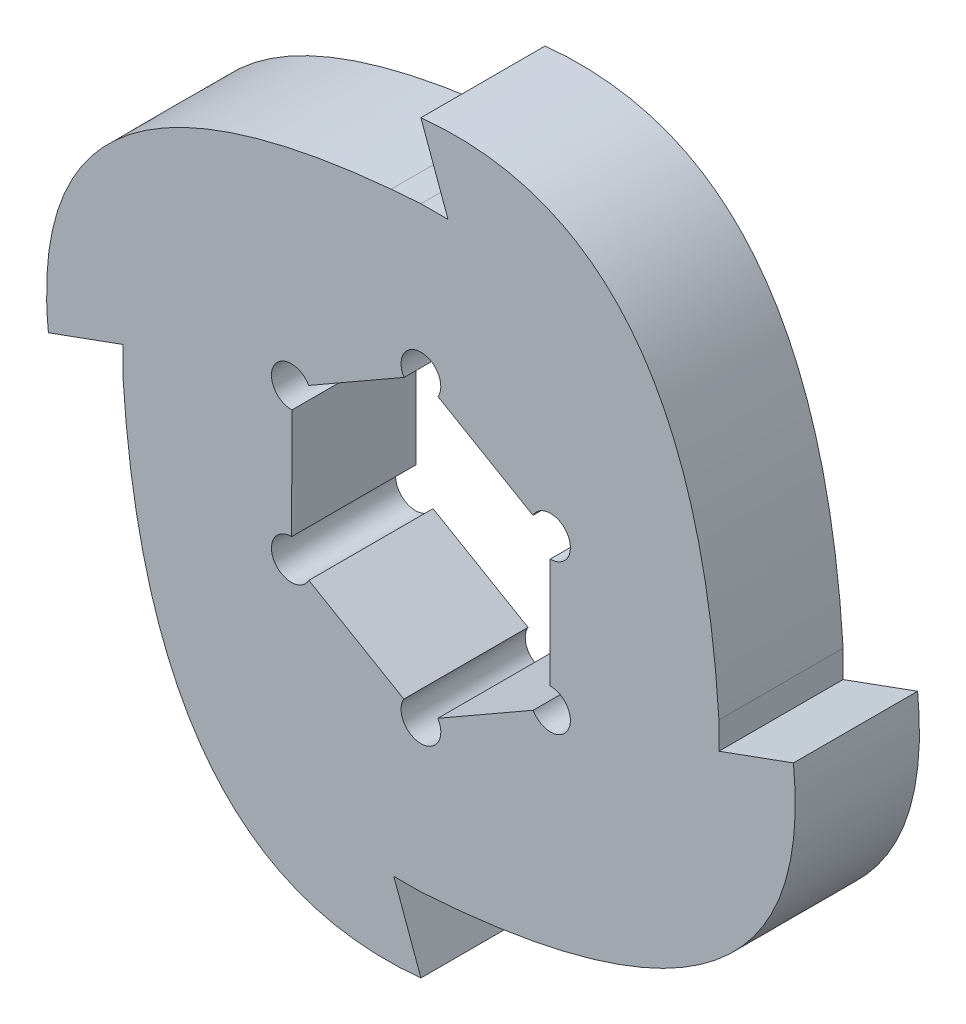
SolidWorks part; units mm, degrees
material "ASTM A36 Steel"
ref_plane "Front Plane" through (0, 0, 0) normal (0, 0, 1) x (1, 0, 0)
ref_plane "Top Plane" through (0, 0, 0) normal (0, 1, 0) x (1, 0, 0)
ref_plane "Right Plane" through (0, 0, 0) normal (1, 0, 0) x (0, 0, -1)
sketch "Sketch1" plane through (0, 0, 0) normal (0, 0, 1) x (1, 0, 0)
  line L0 (0, -1038.1) -> (0, -19.05) construction
  line L1 (6.595, -2.811) -> (6.6131, 2.8106)
  line L2 (5.7319, 4.3059) -> (0.8725, 7.1324)
  line L3 (-0.8631, 7.1169) -> (-5.7406, 4.3218)
  line L4 (-6.595, 2.811) -> (-6.6131, -2.8106)
  line L5 (-5.7319, -4.3059) -> (-0.8725, -7.1324)
  line L6 (0.8631, -7.1169) -> (5.7406, -4.3218)
  line L11 (0, 8.669) -> (0, 15.24) construction
  line L12 (0, 19.05) -> (0, 29.6546) construction
  line L13 (0, -7.653) -> (0, 7.653) construction
  line L14 (-19.05, 0) -> (-15.24, 1.3867)
  line L15 (-15.24, 1.3867) -> (-15.24, 0)
  line L16 (1.3867, 15.24) -> (0, 15.24)
  line L17 (0, 19.05) -> (1.3867, 15.24)
  line L18 (15.24, -1.3867) -> (15.24, 0)
  line L19 (19.05, 0) -> (15.24, -1.3867)
  line L20 (-1.3867, -15.24) -> (0, -15.24)
  line L21 (0, -19.05) -> (-1.3867, -15.24)
  line L22 (0, -15.24) -> (0, -8.669) construction
  circle A0 centre (0, 0) radius 19.05 construction
  circle A1 centre (0, 0) radius 6.604 construction
  arc A2 (-5.7406, 4.3218) -> (-6.595, 2.811) centre (-6.6277, 3.8265) ccw
  arc A3 (0.8725, 7.1324) -> (-0.8631, 7.1169) centre (0, 7.653) ccw
  arc A4 (6.6131, 2.8106) -> (5.7319, 4.3059) centre (6.6277, 3.8265) ccw
  arc A5 (5.7406, -4.3218) -> (6.595, -2.811) centre (6.6277, -3.8265) ccw
  arc A6 (-0.8725, -7.1324) -> (0.8631, -7.1169) centre (0, -7.653) ccw
  arc A7 (-6.6131, -2.8106) -> (-5.7319, -4.3059) centre (-6.6277, -3.8265) ccw
  spline S0 degree 2 poles (-15.24, 0) (-13.9321, -20.4786) (0, -19.05) knots 0 0 0 0.635746 0.635746 0.635746
  spline S1 degree 3 poles (-1.5242, 15.1224) (-14.1243, 13.9761) (-19.9662, 8.9353) (-19.05, 0) knots 0.024149 0.024149 0.024149 0.024149 0.635746 0.635746 0.635746 0.635746
  spline S2 degree 2 poles (15.24, 0) (13.9321, 20.4786) (0, 19.05) knots 0 0 0 0.635746 0.635746 0.635746
  spline S3 degree 2 poles (0, -15.24) (20.4786, -13.9321) (19.05, 0) knots 0 0 0 0.635746 0.635746 0.635746
  spline S4 degree 2 poles (0, 15.24) (-20.4786, 13.9321) (-19.05, 0) knots 0 0 0 0.635746 0.635746 0.635746
  spline S5 degree 2 poles (15.24, 0) (13.9321, 20.4786) (0, 19.05) knots 0 0 0 0.635746 0.635746 0.635746
  spline S6 degree 2 poles (0, -15.24) (20.4786, -13.9321) (19.05, 0) knots 0 0 0 0.635746 0.635746 0.635746
  point P27 (0, 0)
  point P33 (0, 0)
  point P44 (0, 0)
  point P53 (0, 0)
  dimension "D1" = 38.1
  dimension "D6" = 1.016
  dimension "D2" = 6.604
  dimension "D4" = 3.81
  dimension "D3" = 70
  dimension "D5" = 4
  dimension "D7" = 6
extrude "Boss-Extrude2" add sketch "Sketch1" along normal blind 6.35
